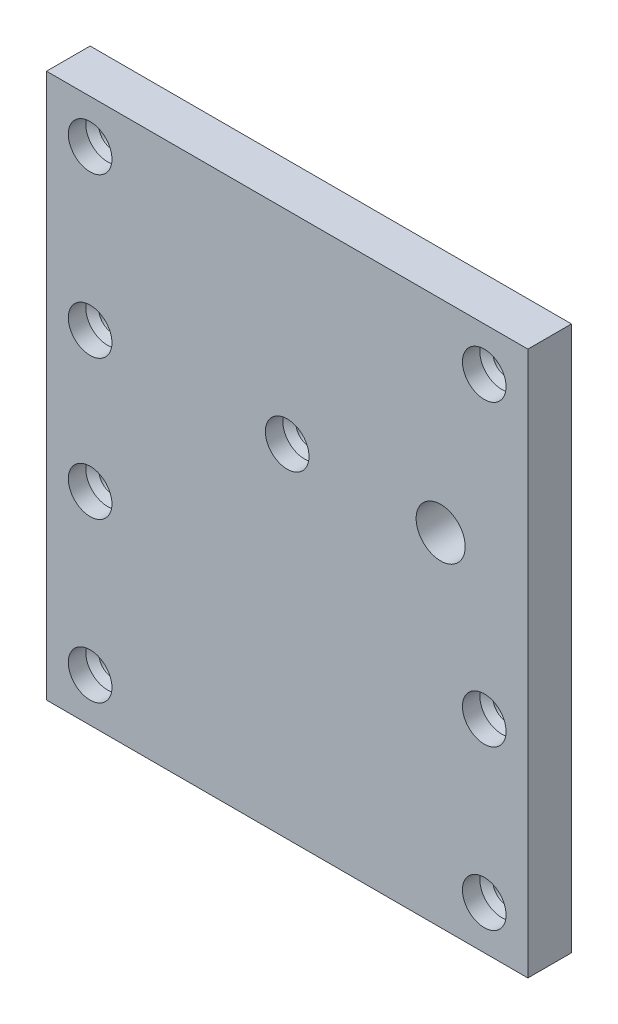
SolidWorks part; units mm, degrees
material "PET"
ref_plane "Front Plane" through (0, 0, 0) normal (0, 0, 1) x (1, 0, 0)
ref_plane "Top Plane" through (0, 0, 0) normal (0, 1, 0) x (1, 0, 0)
ref_plane "Right Plane" through (0, 0, 0) normal (1, 0, 0) x (0, 0, -1)
sketch "Sketch1" plane through (0, 0, 0) normal (0, 0, 1) x (1, 0, 0)
  line L1 (20.3421, 15.5299) -> (-14.7, 15.5299)
  line L2 (20.3421, 15.5299) -> (20.3421, 55.1793)
  line L3 (20.3421, 55.1793) -> (-14.7, 55.1793)
  line L4 (-14.7, 15.5299) -> (-14.7, 55.1793)
extrude "Boss-Extrude1" add sketch "Sketch1" along normal blind 3.175
hole_wizard "9/64 (0.14063) Diameter Hole1" positions "Sketch3" profile "Sketch2" hole size "9/64" standard "ANSI Inch" end condition through all
sketch "Sketch3" plane through (0, 0, 3.175) normal (0, 0, 1) x (1, 0, 0)
  point P0 (13.9921, 40.4346)
sketch "Sketch2" plane through (13.9921, 40.4346, 3.175) normal (1, 0, 0) x (0, -1, 0)
  line L0 (0, 0) -> (0, 3.175)
  line L1 (0, 3.175) -> (1.786, 3.175)
  line L2 (1.786, 3.175) -> (1.786, 0)
  line L5 (1.786, 0) -> (0, 0)
  line L11 (0, -6.35) -> (0, 107.95) construction
  dimension "Thru Hole Dia." = 3.572
  dimension "Thru Hole Depth" = 3.175
hole_wizard "5/64 (0.07813) Diameter Hole1" positions "Sketch5" profile "Sketch4" hole size "5/64" standard "ANSI Inch" end condition through all
sketch "Sketch5" plane through (0, 0, 3.175) normal (0, 0, 1) x (1, 0, 0)
  line L0 (-14.7, 37.2596) -> (20.3421, 37.2596) construction
  line L1 (-14.7, 55.1793) -> (-14.7, 37.2596) construction
  line L2 (2.8211, 55.1793) -> (2.8211, 15.5299) construction
  line L3 (20.3421, 55.1793) -> (-14.7, 55.1793) construction
  line L4 (-14.7, 15.5299) -> (20.3421, 15.5299) construction
  line L5 (2.8211, 35.3546) -> (20.3421, 35.3546) construction
  line L6 (20.3421, 15.5299) -> (20.3421, 55.1793) construction
  point P0 (-11.525, 40.4346)
  point P14 (-11.525, 52.0043)
  point P19 (17.1671, 52.0043)
  point P20 (2.8211, 40.4346)
  point P29 (-11.525, 30.2746)
  point P30 (-11.525, 18.7049)
  point P31 (17.1671, 18.7049)
  point P32 (17.1671, 30.2746)
  dimension "D1" = 3.175
  dimension "D2" = 3.175
  dimension "D3" = 3.175
sketch "Sketch4" plane through (-11.525, 40.4346, 3.175) normal (1, 0, 0) x (0, -1, 0)
  line L0 (0, 0) -> (0, 3.175)
  line L1 (0, 3.175) -> (0.9923, 3.175)
  line L2 (0.9923, 3.175) -> (0.9923, 0)
  line L5 (0.9923, 0) -> (0, 0)
  line L11 (0, -6.35) -> (0, 107.95) construction
  dimension "Thru Hole Dia." = 1.9845
  dimension "Thru Hole Depth" = 3.175
hole_wizard "1/8 (0.125) Diameter Hole1" positions "Sketch7" profile "Sketch8" hole size "1/8" standard "ANSI Inch"
sketch "Sketch7" plane through (0, 0, 3.175) normal (0, 0, 1) x (1, 0, 0)
  point P0 (17.1671, 18.7049)
  point P3 (-11.525, 18.7049)
  point P6 (-11.525, 30.2746)
  point P9 (17.1671, 30.2746)
  point P12 (2.8211, 40.4346)
  point P16 (-11.525, 40.4346)
  point P23 (17.1671, 52.0043)
  point P26 (-11.525, 52.0043)
sketch "Sketch8" plane through (17.1671, 18.7049, 3.175) normal (1, 0, 0) x (0, -1, 0)
  line L0 (0, 0) -> (0, 2.2239)
  line L1 (0, 2.2239) -> (1.5875, 1.27)
  line L2 (1.5875, 1.27) -> (1.5875, 0)
  line L5 (1.5875, 0) -> (0, 0)
  line L10 (0, 2.2239) -> (-1.5875, 1.27) construction
  line L11 (0, -6.35) -> (0, 107.95) construction
  dimension "Hole Dia." = 3.175
  dimension "Hole Depth" = 1.27
  dimension "Drill Angle" = 118
mirror "Mirror1" [suppressed]
delete or keep bodies "Body-Delete/Keep 1" [suppressed] type delete bodies bodies 104
